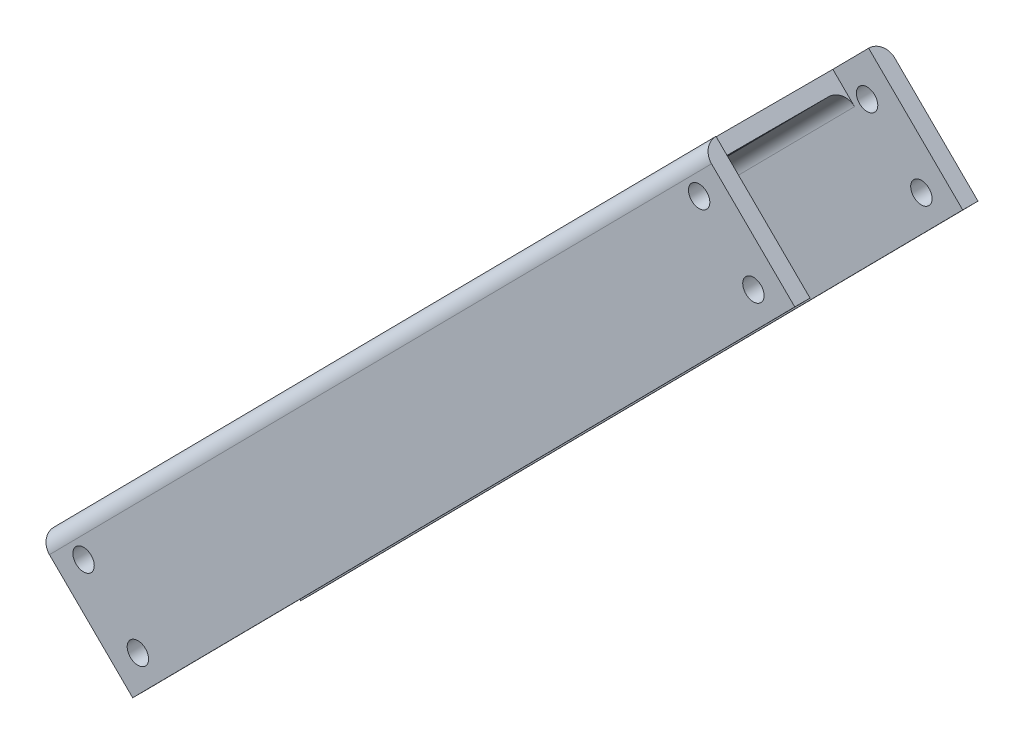
SolidWorks part; units mm, degrees
ref_plane "Front Plane" through (0, 0, 0) normal (0, 0, 1) x (1, 0, 0)
ref_plane "Top Plane" through (0, 0, 0) normal (0, 1, 0) x (1, 0, 0)
ref_plane "Right Plane" through (0, 0, 0) normal (1, 0, 0) x (0, 0, -1)
sketch "Sketch2" plane through (0, 0, 0) normal (0, 0, 1) x (1, 0, 0)
  line L0 (165.715, 148.457) -> (35.6364, 16.9102)
  line L1 (35.6364, 16.9102) -> (54.1241, -1.3711)
  line L4 (54.1241, -1.3711) -> (184.2027, 130.1757)
  line L25 (165.715, 148.457) -> (184.2027, 130.1757)
extrude "Boss-Extrude1" add sketch "Sketch2" against normal blind 3
sketch "Sketch4" plane through (0, 0, -36) normal (0, 0, -1) x (-1, 0, 0)
  line L6 (-165.715, 148.457) -> (-184.2027, 130.1757)
  line L9 (-184.2027, 130.1757) -> (-54.1241, -1.3711)
  line L10 (-54.1241, -1.3711) -> (-35.6364, 16.9102)
  line L11 (-35.6364, 16.9102) -> (-165.715, 148.457)
  line L12 (-165.715, 148.457) -> (-184.2027, 130.1757)
  line L15 (-184.2027, 130.1757) -> (-54.1241, -1.3711)
  line L16 (-54.1241, -1.3711) -> (-35.6364, 16.9102)
  line L17 (-35.6364, 16.9102) -> (-165.715, 148.457)
  dimension "D1" = 0
extrude "Boss-Extrude2" add sketch "Sketch4" against normal blind 3 separate body
sketch "Sketch5" plane through (0, 0, -3) normal (0, 0, -1) x (-1, 0, 0)
  line L0 (-35.6364, 16.9102) -> (-165.715, 148.457) construction
  line L1 (-35.6364, 16.9102) -> (-165.715, 148.457)
  line L2 (-37.7696, 14.8008) -> (-167.8482, 146.3476)
  line L3 (-37.7696, 14.8008) -> (-35.6364, 16.9102)
  line L4 (-167.8482, 146.3476) -> (-165.715, 148.457)
  dimension "D1" = 3
extrude "Boss-Extrude3" add sketch "Sketch5" along normal up to surface (30 mm away)
fillet "Fillet1" radius 3
sketch "Sketch6" plane through (9.5636, -9.4569, 0) normal (-0.7111, 0.7031, 0) x (0, 0, 1)
  circle A0 centre (-18, 197.0812) radius 7.5
extrude "Cut-Extrude1" cut sketch "Sketch6" against normal up to surface (3 mm away)
sketch "Sketch7" plane through (9.5636, -9.4569, 0) normal (-0.7111, 0.7031, 0) x (0, 0, 1)
  line L5 (-3, 37.0812) -> (-3, 222.0812) construction
  line L6 (-3, 212.0812) -> (-3, 222.0812)
  line L7 (-33, 222.0812) -> (-33, 37.0812) construction
  line L8 (-33, 222.0812) -> (-33, 212.0812)
  line L9 (-33, 212.0812) -> (-3, 212.0812)
  line L12 (-33, 222.0812) -> (-3, 222.0812)
  line L13 (-36, 129.5812) -> (0, 129.5812) construction
  line L14 (-36, 37.0812) -> (-36, 222.0812) construction
  line L15 (0, 222.0812) -> (0, 37.0812) construction
  line L16 (-33, 37.0812) -> (-3, 37.0812)
  line L17 (-33, 47.0812) -> (-3, 47.0812)
  line L18 (-33, 37.0812) -> (-33, 47.0812)
  line L19 (-3, 47.0812) -> (-3, 37.0812)
extrude "Cut-Extrude2" cut sketch "Sketch7" against normal up to surface (26 mm away)
sketch "Sketch8" plane through (0, 0, 0) normal (0, 0, 1) x (1, 0, 0)
  line L0 (58.6944, 3.2508) -> (40.2067, 21.5321) construction
  line L5 (179.6323, 125.5538) -> (161.1447, 143.8351) construction
  line L6 (158.6837, 141.3464) -> (165.715, 148.457) construction
  line L8 (100.6757, 82.6836) -> (119.1634, 64.4023) construction
  line L9 (42.6677, 24.0208) -> (158.6837, 141.3464) construction
  line L10 (54.1241, -1.3711) -> (184.2027, 130.1757) construction
  circle A0 centre (176.077, 129.0694) radius 2.1
  circle A1 centre (165.4111, 139.6163) radius 2.1
  circle A2 centre (44.4731, 17.3134) radius 2.1
  circle A3 centre (55.1391, 6.7664) radius 2.1
extrude "Cut-Extrude3" cut sketch "Sketch8" against normal up to surface (36 mm away)
fillet "Fillet2" radius 1
